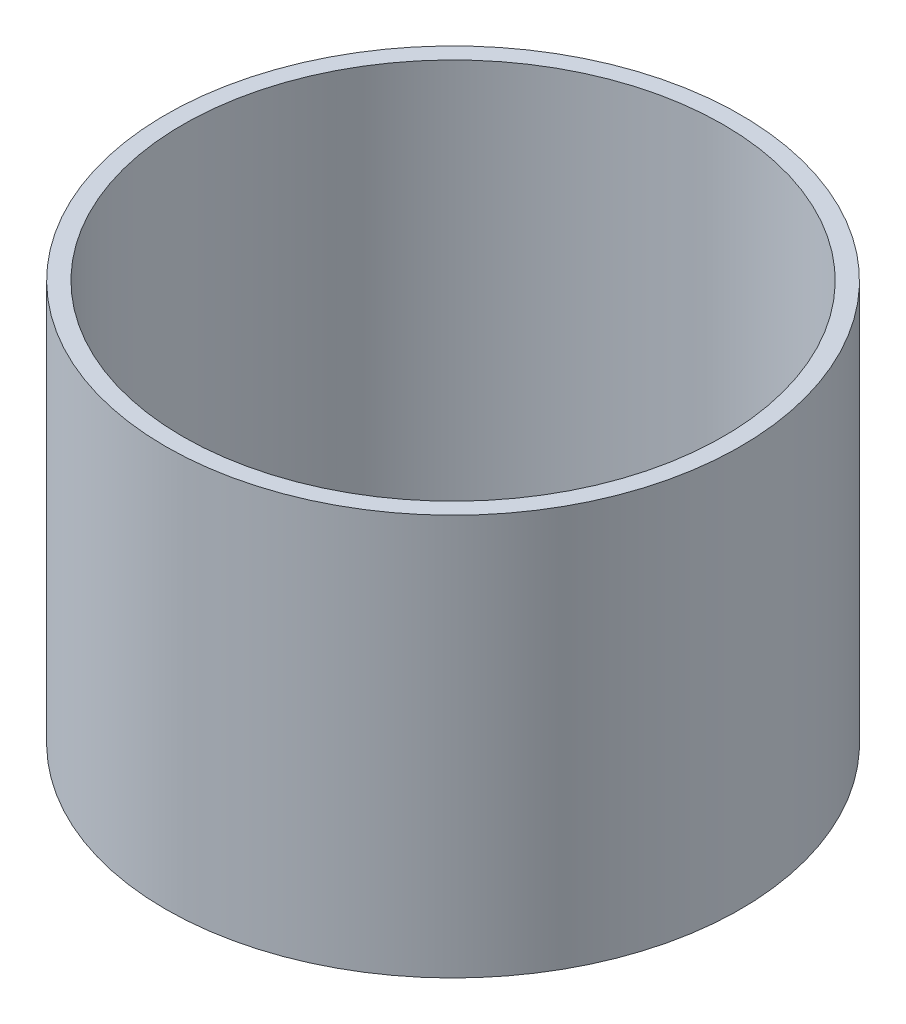
SolidWorks part; units mm, degrees
material "PVC rigide"
ref_plane "Plan de face" through (0, 0, 0) normal (0, 0, 1) x (1, 0, 0)
ref_plane "Plan de dessus" through (0, 0, 0) normal (0, 1, 0) x (1, 0, 0)
ref_plane "Plan de droite" through (0, 0, 0) normal (1, 0, 0) x (0, 0, -1)
sketch "Esquisse1" plane through (0, 0, 0) normal (0, 1, 0) x (1, 0, 0)
  circle A0 centre (0, 0) radius 47.2
  circle A1 centre (0, 0) radius 50.2
  dimension "D1" = 94.4
  dimension "D2" = 100.4
extrude "Boss.-Extru.1" add sketch "Esquisse1" along normal blind 70
